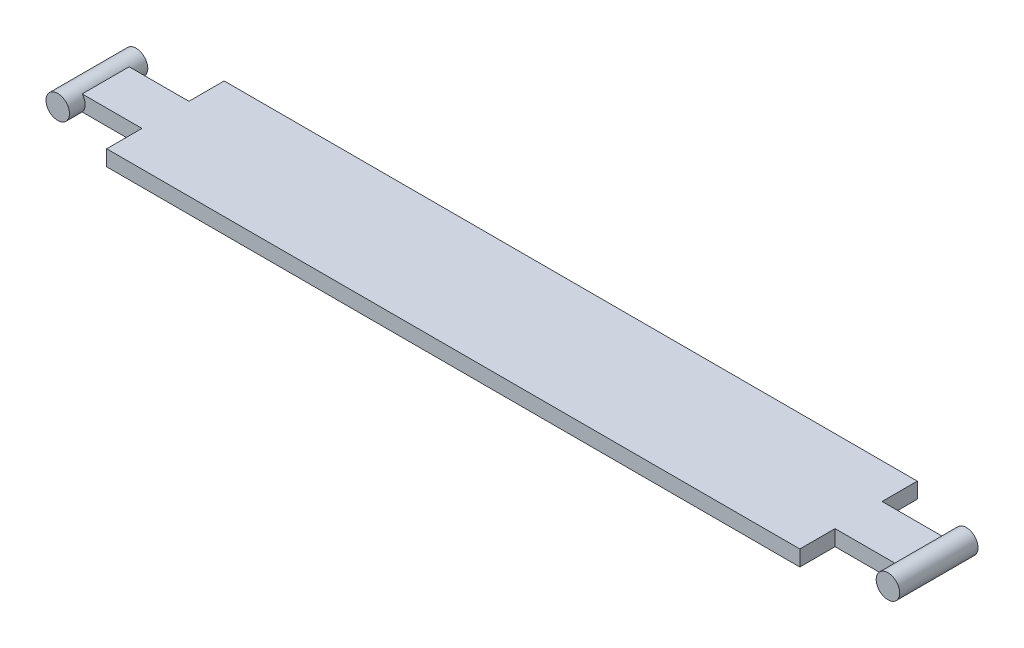
SolidWorks part; units mm, degrees
ref_plane "前视基准面" through (0, 0, 0) normal (0, 0, 1) x (1, 0, 0)
ref_plane "上视基准面" through (0, 0, 0) normal (0, 1, 0) x (1, 0, 0)
ref_plane "右视基准面" through (0, 0, 0) normal (1, 0, 0) x (0, 0, -1)
sketch "草图1" plane through (0, 0, 0) normal (0, 1, 0) x (1, 0, 0)
  line L0 (0, 0) -> (0, 4.5) construction
  line L1 (44.25, 7.5) -> (-44.25, 7.5)
  line L2 (53, 3) -> (53, -3)
  line L3 (44.25, -7.5) -> (-44.25, -7.5)
  line L4 (-53, 3) -> (-53, -3)
  line L9 (53, -3) -> (44.25, -3)
  line L10 (44.25, -7.5) -> (44.25, -3)
  line L13 (53, 3) -> (44.25, 3)
  line L14 (44.25, 7.5) -> (44.25, 3)
  line L17 (-53, 3) -> (-44.25, 3)
  line L18 (-44.25, 7.5) -> (-44.25, 3)
  line L21 (-53, -3) -> (-44.25, -3)
  line L22 (-44.25, -7.5) -> (-44.25, -3)
  line L23 (0, 0) -> (19.1336, 0) construction
  point P0 (0, 0)
  dimension "D1" = 106
  dimension "D2" = 15
  dimension "D3" = 88.5
  dimension "D4" = 6
extrude "凸台-拉伸1" add sketch "草图1" along normal blind 2
sketch "草图2" plane through (0, 0, 0) normal (0, 0, 1) x (1, 0, 0)
  line L0 (-53, 2) -> (-53, 0) construction
  line L1 (53, 2) -> (53, 0) construction
  circle A0 centre (-53, 1) radius 1.5
  circle A1 centre (53, 1) radius 1.5
  dimension "D1" = 3
extrude "凸台-拉伸2" add sketch "草图2" along normal mid plane 10
